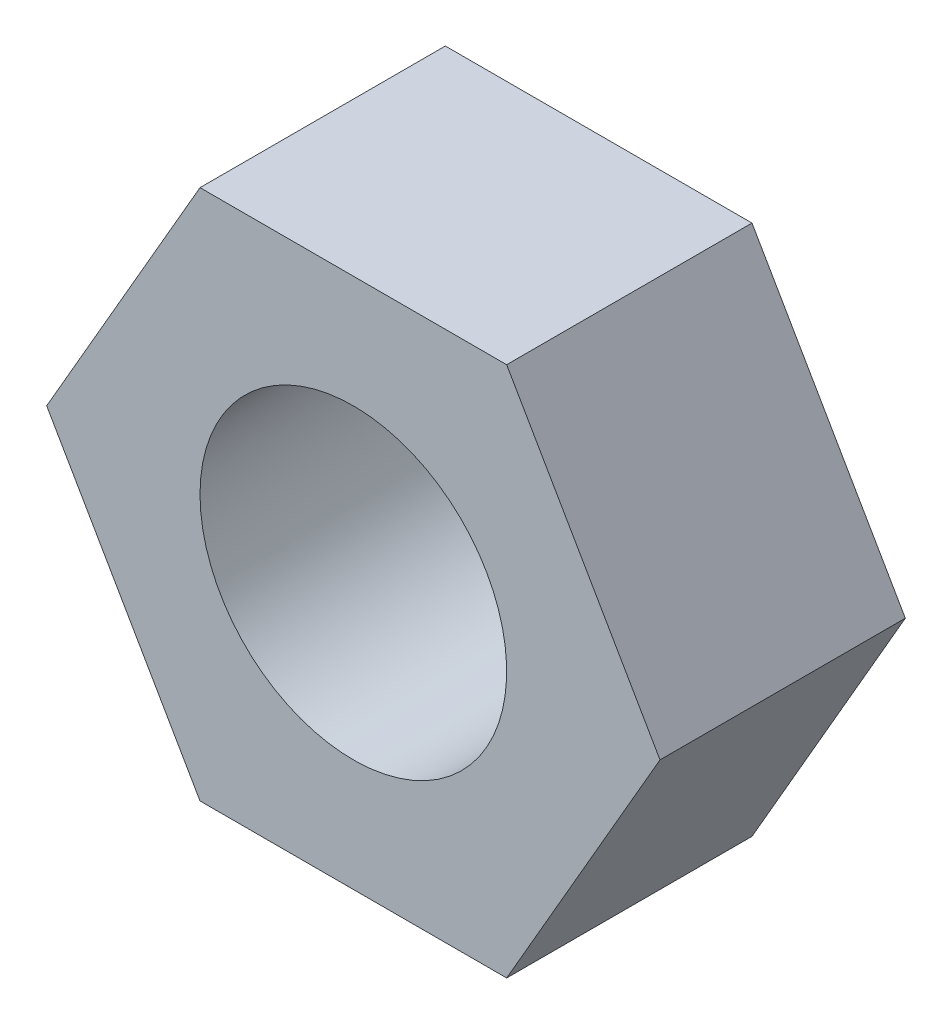
SolidWorks part; units mm, degrees
ref_plane "Alzado" through (0, 0, 0) normal (0, 0, 1) x (1, 0, 0)
ref_plane "Planta" through (0, 0, 0) normal (0, 1, 0) x (1, 0, 0)
ref_plane "Vista lateral" through (0, 0, 0) normal (1, 0, 0) x (0, 0, -1)
sketch "Croquis2" plane through (0, 0, 0) normal (0, 0, 1) x (1, 0, 0)
  line L1 (5, 0) -> (2.5, 4.3301)
  line L2 (2.5, 4.3301) -> (-2.5, 4.3301)
  line L3 (-2.5, 4.3301) -> (-5, 0)
  line L4 (-5, 0) -> (-2.5, -4.3301)
  line L5 (-2.5, -4.3301) -> (2.5, -4.3301)
  line L6 (2.5, -4.3301) -> (5, 0)
  circle A0 centre (0, 0) radius 4.3301 construction
  dimension "D1" = 5
extrude "Saliente-Extruir1" add sketch "Croquis2" along normal blind 4
sketch "Croquis3" plane through (0, 0, 0) normal (0, 0, -1) x (-1, 0, 0)
  circle A0 centre (0, 0) radius 2.5
extrude "Cortar-Extruir1" cut sketch "Croquis3" against normal through all
